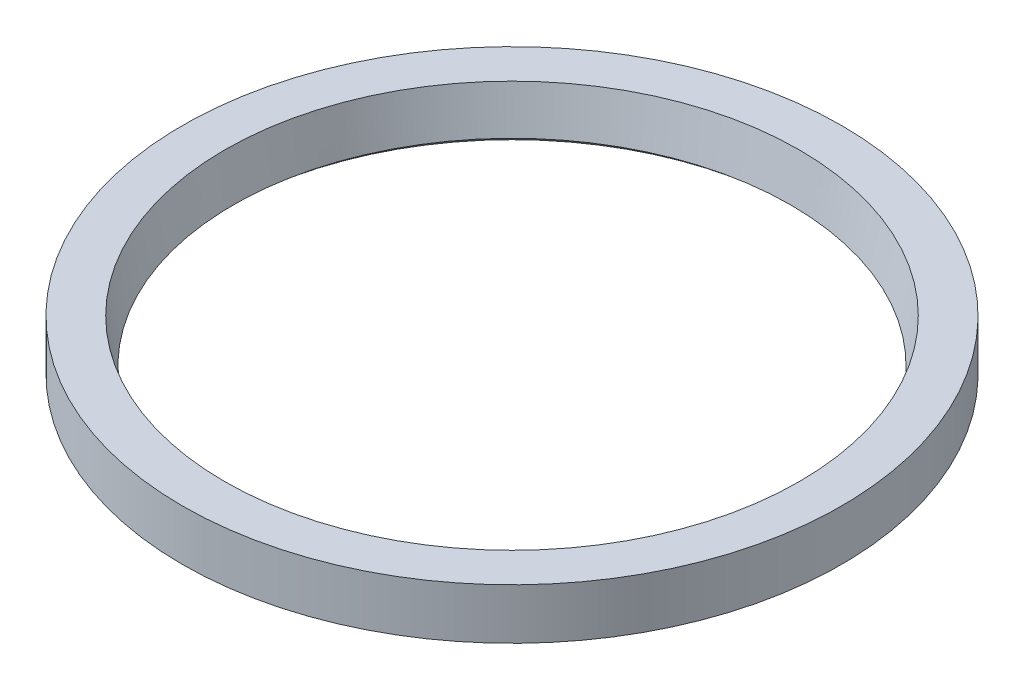
SolidWorks part; units mm, degrees
ref_plane "Piano frontale" through (0, 0, 0) normal (0, 0, 1) x (1, 0, 0)
ref_plane "Piano superiore" through (0, 0, 0) normal (0, 1, 0) x (1, 0, 0)
ref_plane "Piano destro" through (0, 0, 0) normal (1, 0, 0) x (0, 0, -1)
sketch "Schizzo1" plane through (0, 0, 0) normal (0, 0, 1) x (1, 0, 0)
  line L0 (0, 0) -> (17, 0) construction
  line L1 (17, 0) -> (19.5, 0)
  line L2 (19.5, 0) -> (19.5, 3)
  line L3 (19.5, 3) -> (17, 3)
  line L4 (17, 3) -> (16.4887, 0.4348)
  line L5 (16.4887, 0.4348) -> (17, 0)
  line L6 (0, 0) -> (0, 3.4191) construction
  dimension "D1" = 17
  dimension "D2" = 2.5
  dimension "D3" = 3
revolve "Rivoluzione1" add sketch "Schizzo1" angle 360 about L6
